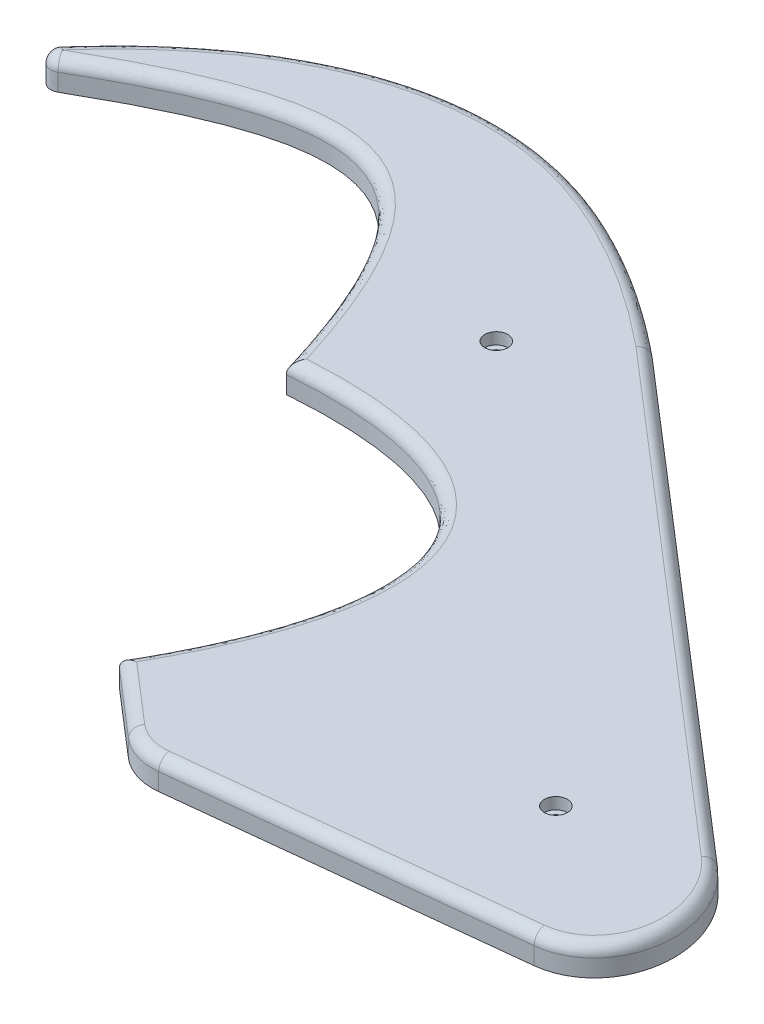
SolidWorks part; units mm, degrees
ref_plane "Front Plane" through (0, 0, 0) normal (0, 0, 1) x (1, 0, 0)
ref_plane "Top Plane" through (0, 0, 0) normal (0, 1, 0) x (1, 0, 0)
ref_plane "Right Plane" through (0, 0, 0) normal (1, 0, 0) x (0, 0, -1)
ref_plane "Plane1" through (0, 10, 0) normal (0, 1, 0) x (1, 0, 0)
sketch "Sketch1" plane through (0, 10, 0) normal (0, 1, 0) x (1, 0, 0)
  line L2 (682.311, -403.8596) -> (741.0033, -397.4501)
  line L3 (663.109, -299.0767) -> (745.362, -369.9947)
  line L4 (674.6955, -401.4924) -> (663.335, -391.6975)
  arc A2 (566.0381, -304.478) -> (568.5304, -307.5398) centre (567.5335, -305.806) ccw
  arc A3 (674.6955, -401.4924) -> (682.311, -403.8596) centre (681.2254, -393.9187) ccw
  spline S3 degree 3 poles (633.7243, -333.1581) (620.3907, -289.5739) (605.3028, -286.3961) (568.5304, -307.5398) knots 0 0 0 0 0.916017 0.916017 0.916017 0.916017
  spline S4 degree 2 poles (741.0033, -397.4501) (743.229, -397.207) (745.1726, -396.2006) (747.1216, -395.1914) (748.5931, -393.514) (750.0176, -391.8901) (750.8577, -389.7927) (751.6567, -387.798) (751.8556, -385.5472) (752.0454, -383.3998) (751.6721, -381.189) (751.311, -379.0507) (750.4485, -377.011) (749.5964, -374.9959) (748.3146, -373.2208) (747.0127, -371.4179) (745.362, -369.9947) knots 0 0 0 0.125 0.125 0.25 0.25 0.375 0.375 0.5 0.5 0.625 0.625 0.75 0.75 0.875 0.875 1 1 1
  spline S5 degree 3 poles (566.0381, -304.478) (586.541, -281.3908) (621.8176, -269.9353) (655.1858, -292.564) (663.109, -299.0767) knots 0.005774 0.005774 0.005774 0.005774 0.670805 1 1 1 1
  spline S6 degree 3 poles (633.7243, -333.1581) (675.5705, -329.9181) (685.5599, -353.3898) (663.335, -391.6975) knots 0 0 0 0 1 1 1 1
extrude "Boss-Extrude1" add sketch "Sketch1" along normal blind 5
fillet "Fillet1" radius 2 9 edges at (565.9824, 15, 307.0686) (678.257, 15, 403.468) (669.0152, 15, 396.5949)
sketch "Sketch3" plane through (0, 10, 0) normal (0, -1, 0) x (1, 0, 0)
  line L0 (723.8886, 376.5674) -> (640.9865, 305.0899) construction
  line L1 (745.362, 369.9947) -> (663.109, 299.0767) construction
  circle A0 centre (648.9095, 311.9211) radius 1
  circle A2 centre (723.8886, 376.5674) radius 1
  dimension "D2" = 19
  dimension "D3" = 27
  dimension "D1" = 99
extrude "Cut-Extrude1" cut sketch "Sketch3" against normal up to next
sketch "Sketch4" plane through (0, 15, 0) normal (0, 1, 0) x (1, 0, 0)
  circle A0 centre (648.9095, -311.9211) radius 2
  circle A2 centre (723.8886, -376.5674) radius 2
extrude "Cut-Extrude2" cut sketch "Sketch4" against normal blind 2
